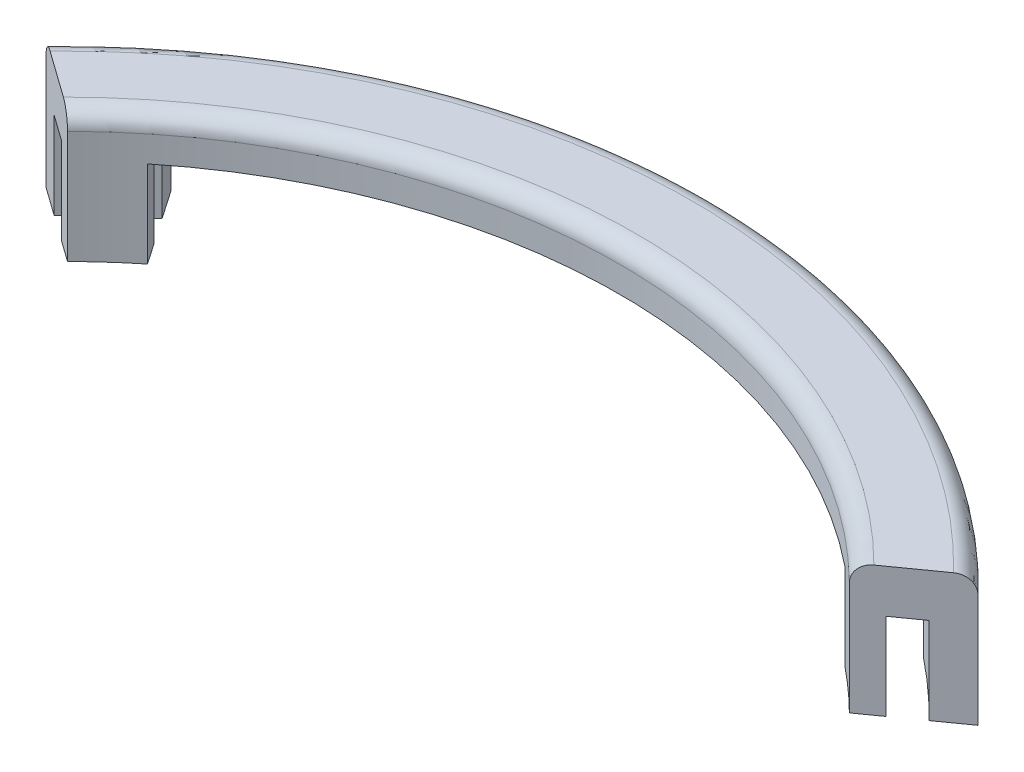
SolidWorks part; units mm, degrees
ref_plane "Front Plane" through (0, 0, 0) normal (0, 0, 1) x (1, 0, 0)
ref_plane "Top Plane" through (0, 0, 0) normal (0, 1, 0) x (1, 0, 0)
ref_plane "Right Plane" through (0, 0, 0) normal (1, 0, 0) x (0, 0, -1)
sketch "Sketch1" plane through (0, 0, 0) normal (0, 1, 0) x (1, 0, 0)
  line L0 (57.2347, 57.7116) -> (68.2256, 65.5535)
  line L1 (-57.2347, 57.7116) -> (-68.2256, 65.5535)
  line L2 (0, 0) -> (0, 94.615) construction
  arc A0 (-68.2256, 65.5535) -> (68.2256, 65.5535) centre (0, 0) cw
  arc A1 (-57.2347, 57.7116) -> (57.2347, 57.7116) centre (0, 0) cw
  dimension "D1" = 94.615
  dimension "D2" = 81.28
  dimension "D4" = 152.4
  dimension "D3" = 127
extrude "Boss-Extrude1" add sketch "Sketch1" along normal blind 19.05
sketch "Sketch3" plane through (0, 0, 0) normal (0, -1, 0) x (1, 0, 0)
  line L0 (-60.3794, -59.9553) -> (-64.0435, -62.5696)
  line L1 (64.0435, -62.5696) -> (60.3794, -59.9553)
  line L2 (57.2347, -57.7116) -> (68.2256, -65.5535) construction
  line L3 (-68.2256, -65.5535) -> (-57.2347, -57.7116) construction
  arc A0 (-64.0435, -62.5696) -> (64.0435, -62.5696) centre (0, 0) ccw
  arc A1 (-60.3794, -59.9553) -> (60.3794, -59.9553) centre (0, 0) ccw
  dimension "D1" = 89.535
  dimension "D2" = 85.09
extrude "Cut-Extrude1" cut sketch "Sketch3" against normal blind 12.7
fillet "Fillet1" radius 2.54 2 edges at (0, 19.05, -81.28) (0, 19.05, -94.615)
sketch "Sketch5" plane through (0, 0, 0) normal (0, 1, 0) x (-1, 0, 0)
  line L0 (-49.6147, -61.1422) -> (-58.9888, -74.7856)
  line L1 (58.9888, -74.7856) -> (49.6147, -61.1422)
  line L3 (60.3794, -59.9553) -> (57.2347, -57.7116) construction
  line L6 (-57.2347, -57.7116) -> (-60.3794, -59.9553) construction
  line L7 (60.3794, -59.9553) -> (57.2347, -57.7116)
  line L8 (-57.2347, -57.7116) -> (-60.3794, -59.9553)
  arc A0 (-58.9888, -74.7856) -> (58.9888, -74.7856) centre (0, 0) ccw
  arc A1 (-49.6147, -61.1422) -> (49.6147, -61.1422) centre (0, 0) ccw
  point P3 (0, 0)
  point P6 (0, 0)
  dimension "D1" = 95.25
  dimension "D2" = 78.74
  dimension "D3" = 20
  dimension "D4" = 20
  dimension "D5" = 7.62
  dimension "D6" = 7.62
extrude "Cut-Extrude2" cut sketch "Sketch5" along normal blind 12.7 contours A1 L0 A0 L1
